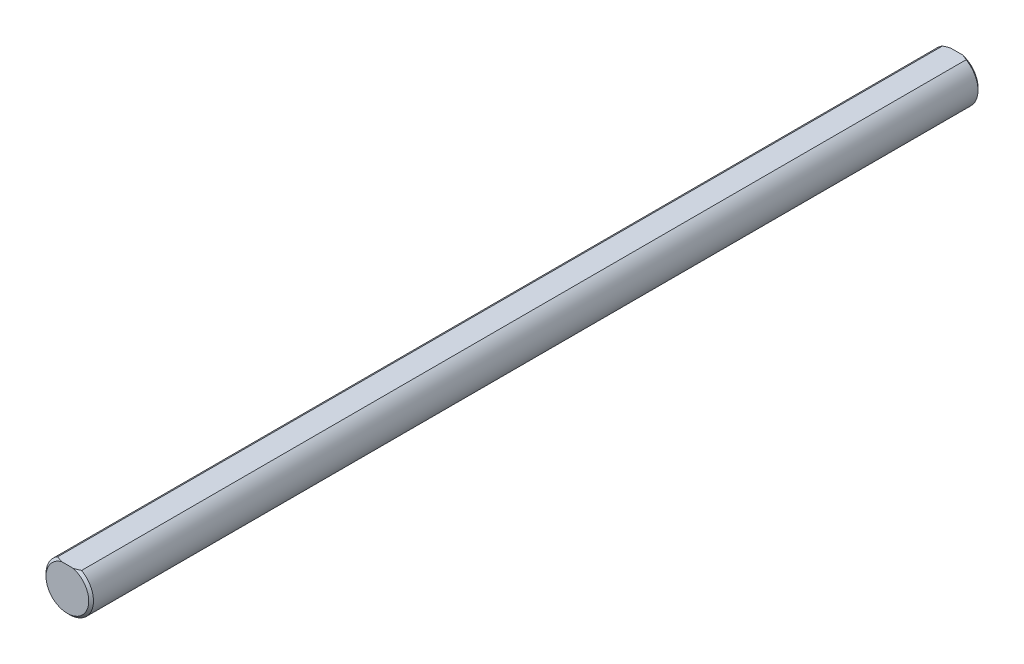
SolidWorks part; units mm, degrees
material "Plain Carbon Steel"
ref_plane "Front Plane" through (0, 0, 0) normal (0, 0, 1) x (1, 0, 0)
ref_plane "Top Plane" through (0, 0, 0) normal (0, 1, 0) x (1, 0, 0)
ref_plane "Right Plane" through (0, 0, 0) normal (1, 0, 0) x (0, 0, -1)
sketch "Sketch1" plane through (0, 0, 0) normal (0, 0, 1) x (1, 0, 0)
  line L0 (-1.5875, 2.7496) -> (1.5875, 2.7496) construction
  circle A1 centre (0, 0) radius 3.175 construction
  dimension "Diameter" = 6.35
  dimension "Flat Width" = 3.175
sketch "Sketch2" plane through (0, 0, 0) normal (1, 0, 0) x (0, 0, -1)
  line L0 (-59.425, 3.175) -> (59.425, 3.175) construction
  line L1 (0, 3.175) -> (0, -3.175) construction
  line L2 (0, 3.175) -> (0, -3.175) construction
  line L3 (-59.425, 3.175) -> (-59.425, -3.175) construction
  line L4 (-59.425, -3.175) -> (59.425, -3.175) construction
  point P2 (0, 3.175)
  point P3 (46.725, 3.175)
  point P4 (-46.725, 3.175)
  dimension "Length" = 118.85
  dimension "D2" = 12.7
  dimension "D1" = 12.7
  dimension "D-Profile Length" = 118.85
sketch "Sketch3" plane through (0, 0, 0) normal (0, 0, 1) x (1, 0, 0)
  circle A1 centre (0, 0) radius 3.175 construction
  circle A3 centre (0, 0) radius 3.175
extrude "Boss-Extrude2" add sketch "Sketch3" along normal up to vertex (59.425 mm away) and the other way up to vertex (59.425 mm away) up to point (0, 3.175, 59.425) other way up to point (0, 3.175, -59.425)
sketch "Sketch10" plane through (0, 0, 0) normal (0, 0, 1) x (1, 0, 0)
  line L0 (-1.5875, 2.7496) -> (1.5875, 2.7496)
  line L1 (0, 0) -> (0, 3.175) construction
  circle A0 centre (0, 0) radius 3.175 construction
  circle A1 centre (0, 0) radius 3.175 construction
  arc A2 (-1.5875, 2.7496) -> (1.5875, 2.7496) centre (0, 0) cw
extrude "Cut-Extrude5" cut sketch "Sketch10" against normal through all both and the other way through all
chamfer "Chamfer1" distance 0.3175 angle 45 4 edges at (0, -3.175, 59.425) (0, -3.175, -59.425) (0, 2.7496, -59.425) (0, 2.7496, 59.425)
equation "\"D1@Chamfer1\"= \"Diameter@Sketch1\" / 20"
equation "\"D1@Sketch2\"=\"Diameter@Sketch1\"*2"
equation "\"D2@Sketch2\"=\"D1@Sketch2\""
